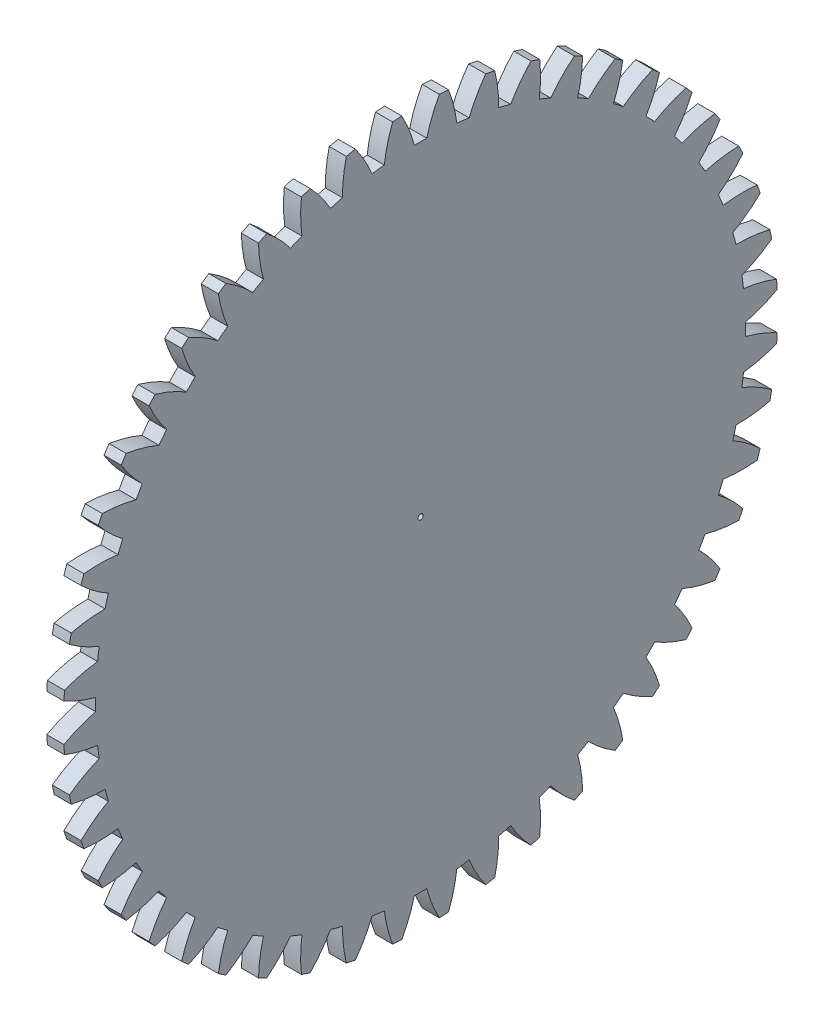
SolidWorks part; units mm, degrees
ref_plane "Plane1" through (0, 0, 0) normal (0, 0, 1) x (1, 0, 0)
ref_plane "Plane2" through (0, 0, 0) normal (0, 1, 0) x (1, 0, 0)
ref_plane "Plane3" through (0, 0, 0) normal (1, 0, 0) x (0, 0, -1)
sketch "HoldingSke" plane through (0, 0, 0) normal (0, 1, 0) x (1, 0, 0)
  line L0 (0, 0) -> (0.2677, -0.2973)
  line L1 (-15, 0) -> (100, 0) construction
  line L2 (0, 0) -> (-2.1039, 2.3779)
  line L3 (0, 0) -> (-11.863, 4.5341)
  line L4 (0, 0) -> (5.7786, 6.4178)
  line L5 (0, 0) -> (-46.8476, -17.4728)
  line L6 (0, 0) -> (-2.4869, -1.6779)
  line L7 (-2.1039, 2.3779) -> (8.6586, 51.2059)
  line L8 (-76.2, 54.61) -> (-76.1, 54.61)
  line L9 (-71.009, 38.7566) -> (-53.1078, 45.2721)
  line L10 (-76.2, 71.12) -> (104.1128, 71.12)
  line L11 (0, 0) -> (-3, 0)
  line L12 (-76.2, 101.6) -> (-76.113, 101.6)
  line L13 (24.9733, 27.94) -> (52.9518, 28.4284)
  line L14 (24.9733, 27.94) -> (24.9743, 27.94)
  line L15 (24.9733, 27.94) -> (100.4006, 29.5858)
  line L16 (-63.627, -2.5) -> (-12.827, -2.5)
  circle A0 centre (0, 0) radius 0.45
  circle A1 centre (0, 0) radius 37.5
  circle A2 centre (0, 0) radius 37.5
  circle A3 centre (0, 0) radius 0.45
  dimension "MHD" = 75
  dimension "Hub_dia" = 75
  dimension "Bore" = 0.9
  dimension "MBD" = 0.9
  dimension "Num_teeth" = 48
  dimension "Pitch" = 0.4
  dimension "Overall_len" = 50
  dimension "Show_teeth" = 48
  dimension "Thickness" = 3
  dimension "OAL" = 50.0001
  dimension "T_dim" = 0.1
  dimension "Ap" = 20
  dimension "H" = 19.05
  dimension "Pitch_radius" = 180.3128
  dimension "Width" = 3
  dimension "Backlash" = 0.087
  dimension "Addendum_fac" = 1
  dimension "Dedendum_fac" = 1.25
  dimension "Clearance_fac" = 0.25
  dimension "Dedendum_add" = 0.001
  dimension "Module" = 2.5
sketch "BasProSke" plane through (0, 0, 0) normal (0, 1, 0) x (1, 0, 0)
  line L0 (-10, 0) -> (60, 0) construction
  line L1 (0, 0) -> (0, 62.5)
  line L2 (0, 0) -> (3, 0)
  line L3 (3, 0) -> (3, 62.5)
  line L4 (3, 62.5) -> (0, 62.5)
  dimension "Thickness" = 3
  dimension "Diameter" = 125
revolve "Base-Revolve" add sketch "BasProSke" angle 360 about L0
sketch "TooCutSke" plane through (0, 0, 0) normal (1, 0, 0) x (0, 0, -1)
  line L1 (0, 0) -> (0, 107) construction
  line L2 (0, 0) -> (-2.1154, 59.9627) construction
  line L3 (0, 0) -> (-7.8448, 119.6885) construction
  line L4 (-2.1154, 59.9627) -> (-3.9224, 59.8443) construction
  arc A0 (1.0859, 56.8636) -> (-1.0859, 56.8636) centre (0, 0) ccw
  arc A1 (3.2991, 62.4383) -> (-3.2991, 62.4383) centre (0, 0) ccw
  circle A2 centre (0, 0) radius 60 construction
  circle A3 centre (0, 0) radius 56.3816 construction
  arc A4 (-1.0859, 56.8636) -> (-3.2991, 62.4383) centre (-24.3241, 50.8647) ccw
  arc A5 (3.2991, 62.4383) -> (1.0859, 56.8636) centre (24.3241, 50.8647) ccw
  dimension "Root_dia" = 113.748
  dimension "Overcut_dia" = 125.0508
  dimension "Pitch_dia" = 120
  dimension "Base_dia" = 112.7631
  dimension "Flank_rad" = 24
  dimension "Half_ang" = 3.75
  dimension "Half_CT" = 1.8109
extrude "ToothCut" cut sketch "TooCutSke" along normal through all
fillet "Breaks" [suppressed] radius 0.05
fillet "RootFillets" [suppressed] radius 0.626
pattern_circular "TeethCuts" count 48 every 7.5 about axis through (-10, 0, 0) along (1, 0, 0) of "ToothCut", "RootFillets", "Breaks"
sketch "HubNeaOneSke" plane through (0, 0, 0) normal (-1, 0, 0) x (0, 0, 1)
  circle A0 centre (0, 0) radius 37.5
  dimension "Diameter" = 75
extrude "HubNearOne" [suppressed] add sketch "HubNeaOneSke" along normal blind 47.0001
sketch "HubNeaBotSke" plane through (0, 0, 0) normal (-1, 0, 0) x (0, 0, 1)
  circle A0 centre (0, 0) radius 37.5
  dimension "Diameter" = 75
extrude "HubNearBoth" [suppressed] add sketch "HubNeaBotSke" along normal blind 23.5
ref_plane "FarPln" through (3, 0, 0) normal (1, 0, 0) x (0, 0, -1)
sketch "HubFarSke" plane through (3, 0, 0) normal (1, 0, 0) x (0, 0, -1)
  circle A0 centre (0, 0) radius 37.5
  dimension "Diameter" = 75
extrude "HubFar" [suppressed] add sketch "HubFarSke" along normal blind 23.5
sketch "BorSke" plane through (0, 0, 0) normal (1, 0, 0) x (0, 0, -1)
  circle A0 centre (0, 0) radius 0.45
  dimension "Diameter" = 0.9
extrude "Bore" cut sketch "BorSke" along normal mid plane 100.0001
sketch "KeySke" plane through (0, 0, 0) normal (1, 0, 0) x (0, 0, -1)
  line L0 (-0.05, 0) -> (-0.05, 0.55)
  line L1 (-0.05, 0.55) -> (0.05, 0.55)
  line L2 (0.05, 0.55) -> (0.05, 0)
  line L3 (0, 0) -> (0, 34) construction
  line L4 (-0.05, 0) -> (0.05, 0)
  dimension "Offset" = 0.55
  dimension "Width" = 0.1
extrude "Keyway" [suppressed] cut sketch "KeySke" along normal mid plane 100.0001
pattern_circular "Keyway2" [suppressed] count 2 every 90 about axis through (-10, 0, 0) along (1, 0, 0)
equation "' \"Module@HoldingSke\" = 6.35"
equation "' \"Num_teeth@HoldingSke\" = 12"
equation "' \"Ap@HoldingSke\" =  20"
equation "' \"Ap@HoldingSke\" = 20"
equation "' \"Width@HoldingSke\" = 0.5 * 25.4"
equation "' \"Hub_dia@HoldingSke\"= 1 * 25.4"
equation "' \"Hub_dia@HoldingSke\" = 1 * 25.4"
equation "' \"Overall_len@HoldingSke\" = 1.0 * 25.4"
equation "' \"Bore@HoldingSke\" = 0.75 * 25.4"
equation "' \"T_dim@HoldingSke\" = 0.1 * 25.4"
equation "' \"Width@KeySke\" = 0.25 * 25.4"
equation "' \"Show_teeth@HoldingSke\" = 13"
equation "' \"Backlash@HoldingSke\" = 0.009 * 25.4"
equation "' \"Addendum_fac@HoldingSke\" = 1.0"
equation "' \"Dedendum_fac@HoldingSke\" = 1.25"
equation "' \"Dedendum_add@HoldingSke\" = 0.00005 * 25.4"
equation "' \"Clearance_fac@HoldingSke\" = 0.25"
equation "\"Pitch@HoldingSke\" = 1 / \"Module@HoldingSke\""
equation "\"Overcut_dia@TooCutSke\" = (\"Num_teeth@HoldingSke\" + 2 * \"Addendum_fac@HoldingSke\") / \"Pitch@HoldingSke\" + 0.002 * 25.4"
equation "\"Pitch_dia@TooCutSke\" = \"Num_teeth@HoldingSke\" / \"Pitch@HoldingSke\""
equation "\"Base_dia@TooCutSke\" = \"Num_teeth@HoldingSke\" / \"Pitch@HoldingSke\" * cos((\"Ap@HoldingSke\"  * 3.14159265 / 180))"
equation "\"Root_dia@TooCutSke\" = (\"Num_teeth@HoldingSke\" + 2) / \"Pitch@HoldingSke\" - 2 * (\"Addendum_fac@HoldingSke\" + \"Dedendum_fac@HoldingSke\") / \"Pitch@HoldingSke\" - \"Dedendum_add@HoldingSke\" * 2"
equation "\"Half_ang@TooCutSke\" = 180 / \"Num_teeth@HoldingSke\""
equation "\"Half_CT@TooCutSke\" = \"Num_teeth@HoldingSke\" / \"Pitch@HoldingSke\" * sin((3.14159265 / 2 / \"Num_teeth@HoldingSke\")) / 2 - 7 * \"Backlash@HoldingSke\" / 4"
equation "\"Flank_rad@TooCutSke\" = \"Num_teeth@HoldingSke\" / \"Pitch@HoldingSke\" / 5"
equation "\"Radius@RootFillets\" = \"Clearance_fac@HoldingSke\" / \"Pitch@HoldingSke\" + \"Dedendum_add@HoldingSke\""
equation "\"Break_rad@Breaks\" = 0.02 / \"Pitch@HoldingSke\""
equation "\"Thickness@HoldingSke\" = \"Width@HoldingSke\""
equation "\"OAL@HoldingSke\" = \"Thickness@HoldingSke\""
equation "\"MHD@HoldingSke\" = (\"Num_teeth@HoldingSke\" + 2) / \"Pitch@HoldingSke\" - 2 * (\"Addendum_fac@HoldingSke\" + \"Dedendum_fac@HoldingSke\")  / \"Pitch@HoldingSke\" - \"Dedendum_add@HoldingSke\" * 2"
equation "\"MBD@HoldingSke\" = (\"Num_teeth@HoldingSke\" + 2) / \"Pitch@HoldingSke\" - 2 * (\"Addendum_fac@HoldingSke\" + \"Dedendum_fac@HoldingSke\")  / \"Pitch@HoldingSke\" - \"Dedendum_add@HoldingSke\" * 2 - 0.002 * 25.4"
equation "\"MHD@HoldingSke\" = ((sgn( \"MHD@HoldingSke\" - \"Hub_dia@HoldingSke\" )-1)*( \"MHD@HoldingSke\" - \"Hub_dia@HoldingSke\" ))/-2+ \"Hub_dia@HoldingSke\""
equation "\"MBD@HoldingSke\" = ((sgn( \"MBD@HoldingSke\" - \"Bore@HoldingSke\" )-1)*( \"MBD@HoldingSke\" - \"Bore@HoldingSke\" ))/-2+ \"Bore@HoldingSke\""
equation "\"OAL@HoldingSke\" = ((sgn( \"OAL@HoldingSke\" - \"Overall_len@HoldingSke\" )+1)*( \"OAL@HoldingSke\" - \"Overall_len@HoldingSke\" ))/2 + \"Overall_len@HoldingSke\" + 0.000002 * 25.4"
equation "\"Num_teeth@TeethCuts\" = int( \"Show_teeth@HoldingSke\" ) + 1"
equation "\"Num_teeth@TeethCuts\" = ((sgn( \"Num_teeth@TeethCuts\" - \"Num_teeth@HoldingSke\" )-1)*( \"Num_teeth@TeethCuts\" - \"Num_teeth@HoldingSke\" ))/-2+ \"Num_teeth@HoldingSke\""
equation "\"Num_teeth@TeethCuts\" = ((sgn( \"Num_teeth@TeethCuts\" - 2.0)+1)*( \"Num_teeth@TeethCuts\" - 2.0))/2 +2.0"
equation "\"Angle@TeethCuts\" = 360.0 / \"Num_teeth@HoldingSke\""
equation "\"Diameter@BasProSke\" = (\"Num_teeth@HoldingSke\" + 2 * \"Addendum_fac@HoldingSke\") / \"Pitch@HoldingSke\""
equation "\"Thickness@BasProSke\"  = \"Thickness@HoldingSke\""
equation "' \"Fillet_rad@BasProSke\" =  \"Thickness@HoldingSke\" * 0.05"
equation "' \"Fillet_rad@BasProSke\" = \"Thickness@HoldingSke\" * 0.05"
equation "\"MHD@HoldingSke\" = ((sgn( \"MHD@HoldingSke\" - \"Root_dia@TooCutSke\" )-1)*( \"MHD@HoldingSke\" - \"Root_dia@TooCutSke\" ))/-2+ \"Root_dia@TooCutSke\""
equation "\"Diameter@HubNeaOneSke\" = \"MHD@HoldingSke\""
equation "\"Length@HubNearOne\" = \"OAL@HoldingSke\" - \"Thickness@BasProSke\""
equation "\"Diameter@HubNeaBotSke\" = \"MHD@HoldingSke\""
equation "\"Length@HubNearBoth\" = ( \"OAL@HoldingSke\" - \"Thickness@BasProSke\" ) / 2.0"
equation "\"Thickness@FarPln\" = \"Thickness@BasProSke\""
equation "\"Diameter@HubFarSke\" = \"MHD@HoldingSke\""
equation "\"Length@HubFar\" = ( \"OAL@HoldingSke\" - \"Thickness@BasProSke\" ) / 2.0"
equation "\"Diameter@BorSke\" = \"MBD@HoldingSke\""
equation "\"D1@Bore\" = \"OAL@HoldingSke\" * 2.0"
equation "\"D1@Keyway\" = \"OAL@HoldingSke\" * 2.0"
equation "\"Offset@KeySke\" = \"T_dim@HoldingSke\" + \"MBD@HoldingSke\" / 2.0"
